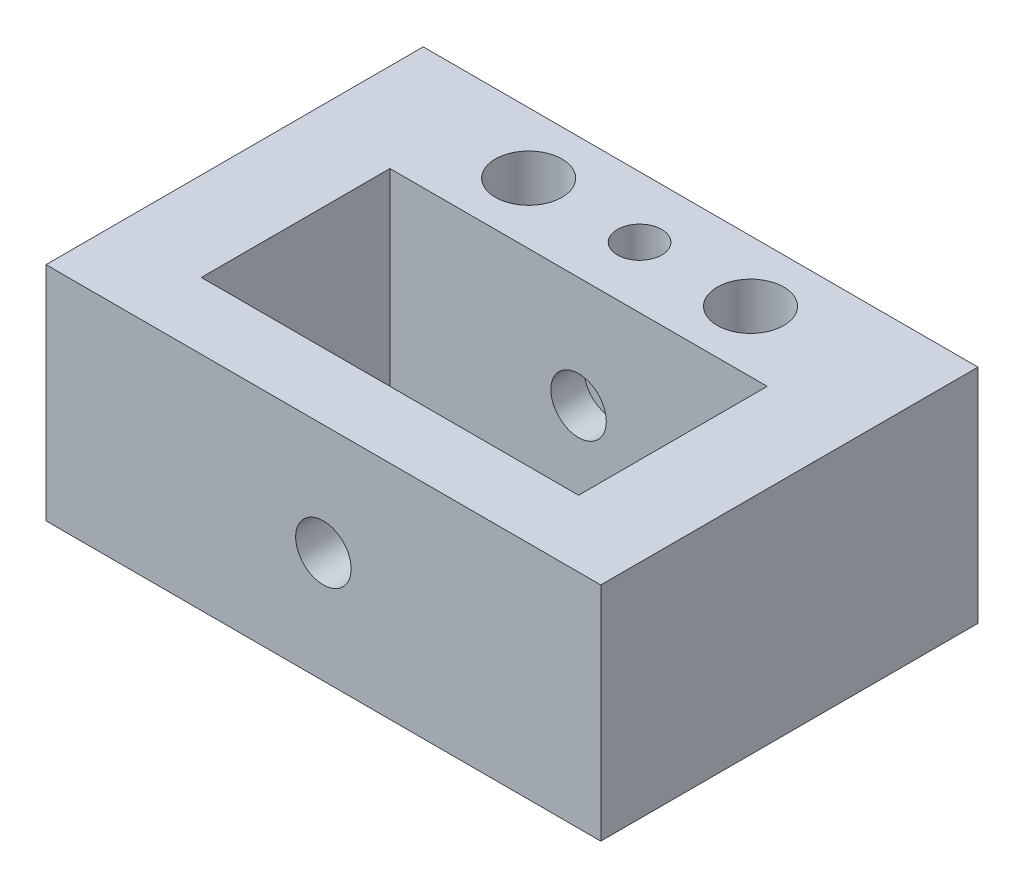
SolidWorks part; units mm, degrees
ref_plane "Front Plane" through (0, 0, 0) normal (0, 0, 1) x (1, 0, 0)
ref_plane "Top Plane" through (0, 0, 0) normal (0, 1, 0) x (1, 0, 0)
ref_plane "Right Plane" through (0, 0, 0) normal (1, 0, 0) x (0, 0, -1)
sketch "Sketch1" plane through (0, 0, 0) normal (0, 0, 1) x (1, 0, 0)
  line L1 (-25, -10) -> (25, -10)
  line L2 (-25, -10) -> (-25, 10)
  line L3 (-25, 10) -> (25, 10)
  line L4 (25, -10) -> (25, 10)
  line L5 (-25, -10) -> (25, 10) construction
  line L6 (-25, 10) -> (25, -10) construction
  point P0 (0, 0)
  dimension "D1" = 50
  dimension "D2" = 20
extrude "Boss-Extrude1" add sketch "Sketch1" along normal blind 11
sketch "Sketch2" plane through (0, 0, 0) normal (0, 0, -1) x (-1, 0, 0)
  circle A2 centre (-20, 0) radius 2
  circle A3 centre (20, 0) radius 2
extrude "Cut-Extrude1" cut sketch "Sketch2" against normal up to surface (11 mm away) up to face at (0, 0, 11)
sketch "Sketch3" plane through (0, -10, 0) normal (0, -1, 0) x (1, 0, 0)
  circle A2 centre (0, 5.5) radius 2
extrude "Cut-Extrude2" cut sketch "Sketch3" against normal through all
sketch "Sketch4" plane through (0, -10, 0) normal (0, -1, 0) x (1, 0, 0)
  circle A2 centre (-10, 5.5) radius 3
  circle A3 centre (10, 5.5) radius 3
extrude "Cut-Extrude3" cut sketch "Sketch4" against normal through all
sketch "Sketch5" plane through (0, 0, 11) normal (0, 0, 1) x (1, 0, 0)
  line L13 (-17, 10) -> (-25, 10)
  line L23 (-25, 10) -> (-25, -10)
  line L24 (-25, -10) -> (-17, -10)
  line L25 (-17, 10) -> (-17, -10)
  line L29 (17, 10) -> (17, -10)
  line L30 (25, -10) -> (17, -10)
  line L31 (25, 10) -> (25, -10)
  line L32 (17, 10) -> (25, 10)
extrude "Boss-Extrude2" add sketch "Sketch5" along normal blind 22
sketch "Sketch13" plane through (0, 0, 11) normal (0, 0, 1) x (1, 0, 0)
  circle A0 centre (0, 0) radius 2.5
extrude "Cut-Extrude6" cut sketch "Sketch13" against normal blind 3
sketch "Sketch14" plane through (0, 0, 33) normal (0, 0, 1) x (1, 0, 0)
  line L0 (25, 10) -> (-25, 10)
  line L1 (-25, 10) -> (-25, -10)
  line L2 (-25, -10) -> (25, -10)
  line L3 (25, -10) -> (25, 10)
extrude "Boss-Extrude4" add sketch "Sketch14" against normal blind 5 and the other way blind 1
sketch "Sketch15" plane through (0, 0, 34) normal (0, 0, 1) x (1, 0, 0)
  circle A0 centre (0, 0) radius 2.5
extrude "Cut-Extrude7" cut sketch "Sketch15" against normal up to surface (6 mm away) up to face at (0, 0, 28)
sketch "Sketch18" plane through (0, 0, 11) normal (0, 0, -1) x (-1, 0, 0)
  circle A0 centre (-20, 0) radius 2
  circle A1 centre (20, 0) radius 2
extrude "Cut-Extrude8" cut sketch "Sketch18" against normal blind 13
